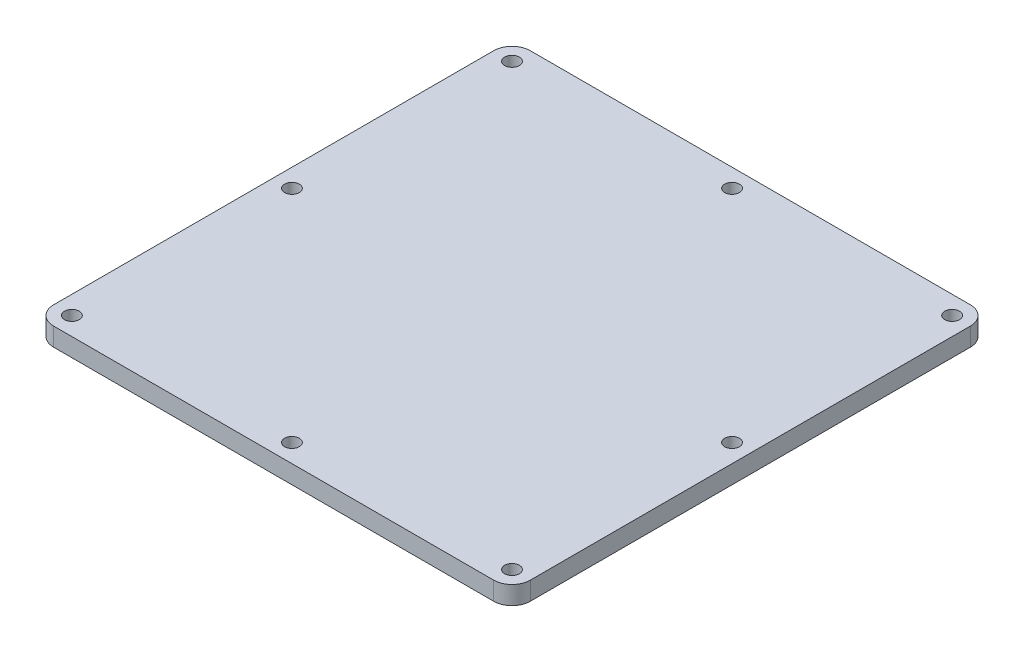
SolidWorks part; units mm, degrees
material "5052-H32"
ref_plane "Front Plane" through (0, 0, 0) normal (0, 0, 1) x (1, 0, 0)
ref_plane "Top Plane" through (0, 0, 0) normal (0, 1, 0) x (1, 0, 0)
ref_plane "Right Plane" through (0, 0, 0) normal (1, 0, 0) x (0, 0, -1)
sketch "Sketch1" plane through (0, 0, 0) normal (0, 1, 0) x (1, 0, 0)
  line L1 (82.55, -82.55) -> (-82.55, -82.55)
  line L2 (82.55, -82.55) -> (82.55, 82.55)
  line L3 (82.55, 82.55) -> (-82.55, 82.55)
  line L4 (-82.55, -82.55) -> (-82.55, 82.55)
  line L5 (82.55, -82.55) -> (-82.55, 82.55) construction
  line L6 (82.55, 82.55) -> (-82.55, -82.55) construction
  point P0 (0, 0)
  point P6 (0, 0)
  dimension "D1" = 165.1
  dimension "D2" = 165.1
extrude "Boss-Extrude1" add sketch "Sketch1" along normal blind 6.35
fillet "Fillet1" radius 6.35 4 edges at (82.55, 3.175, -82.55) (82.55, 3.175, 82.55) (-82.55, 3.175, 82.55) (-82.55, 3.175, -82.55)
hole_wizard "#10 Clearance Hole1" positions "Sketch9" profile "Sketch10" hole size "#10" standard "ANSI Inch" end condition through all
sketch "Sketch9" plane through (0, 6.35, 0) normal (0, 1, 0) x (1, 0, 0)
  line L0 (-76.2, 76.2) -> (76.2, 76.2)
  line L1 (76.2, 76.2) -> (76.2, -76.2)
  line L2 (76.2, -76.2) -> (-76.2, -76.2)
  line L3 (-76.2, -76.2) -> (-76.2, 76.2)
  point P0 (-76.2, -76.2)
  point P3 (-76.2, 76.2)
  point P6 (76.2, 76.2)
  point P9 (76.2, -76.2)
  point P21 (0, 76.2)
  point P23 (0, -76.2)
  point P32 (-76.2, 0)
  point P36 (76.2, 0)
sketch "Sketch10" plane through (-76.2, 6.35, 76.2) normal (1, 0, 0) x (0, 0, 1)
  line L0 (0, 0) -> (0, 6.35)
  line L1 (0, 6.35) -> (2.5527, 6.35)
  line L2 (2.5527, 6.35) -> (2.5527, 0)
  line L5 (2.5527, 0) -> (0, 0)
  line L11 (0, -6.35) -> (0, 107.95) construction
  dimension "Thru Hole Dia." = 5.1054
  dimension "Thru Hole Depth" = 6.35
